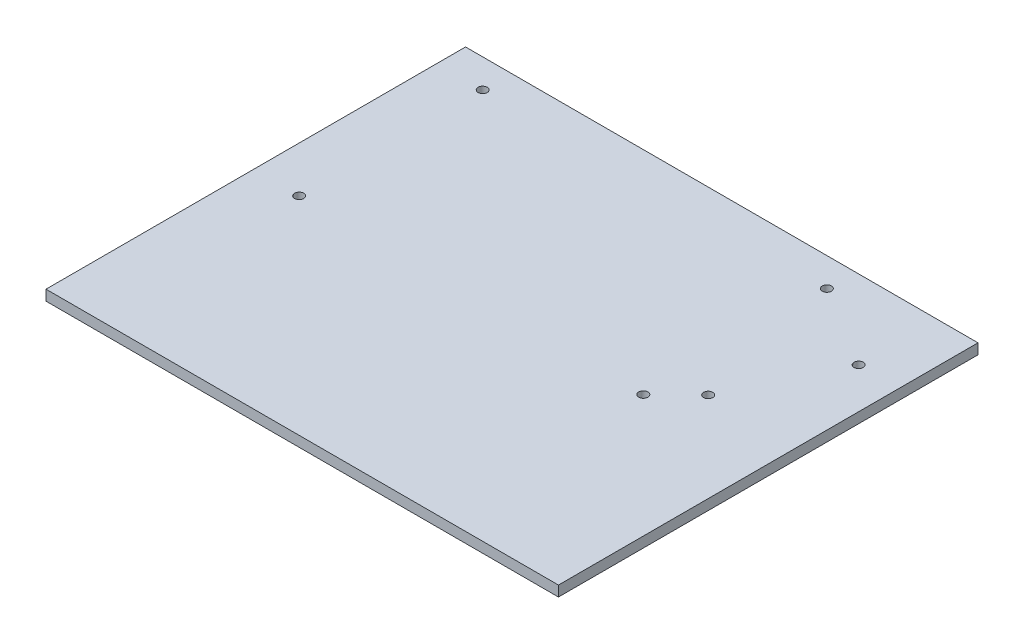
SolidWorks part; units mm, degrees
ref_plane "Front Plane" through (0, 0, 0) normal (0, 0, 1) x (1, 0, 0)
ref_plane "Top Plane" through (0, 0, 0) normal (0, 1, 0) x (1, 0, 0)
ref_plane "Right Plane" through (0, 0, 0) normal (1, 0, 0) x (0, 0, -1)
sketch "Sketch1" plane through (0, 0, 0) normal (0, 1, 0) x (1, 0, 0)
  line L1 (-62.4749, -2.9285) -> (93.8751, -2.9285)
  line L2 (-62.4749, -2.9285) -> (-62.4749, -130.9285)
  line L3 (-62.4749, -130.9285) -> (93.8751, -130.9285)
  line L4 (93.8751, -2.9285) -> (93.8751, -130.9285)
  dimension "D1" = 156.35
  dimension "D2" = 128
extrude "Boss-Extrude1" add sketch "Sketch1" along normal blind 3.175
sketch "Sketch2" plane through (0, 3.175, 0) normal (0, 1, 0) x (1, 0, 0)
  line L0 (-54.1258, -127.6508) -> (-37.2594, -127.6508)
  line L1 (-54.1258, -121.3071) -> (-54.1258, -127.6508)
  line L2 (-37.2594, -121.3071) -> (-54.1258, -121.3071)
  line L3 (-37.2594, -127.6508) -> (-37.2594, -121.3071)
  line L4 (-24.9335, -127.6508) -> (-23.2174, -127.6508)
  line L5 (-24.9335, -121.7955) -> (-24.9335, -127.6508)
  line L6 (-23.2174, -121.7955) -> (-24.9335, -121.7955)
  line L7 (-23.2174, -127.6508) -> (-23.2174, -121.7955)
  line L8 (-12.2222, -127.6508) -> (-9.9317, -127.6508)
  line L9 (-12.2222, -125.2613) -> (-12.2222, -127.6508)
  line L10 (-9.9317, -125.2613) -> (-12.2222, -125.2613)
  line L11 (-9.9317, -127.6508) -> (-9.9317, -125.2613)
  line L12 (-46.5104, -104.2192) -> (-46.5104, -107.6061)
  line L13 (-44.0104, -104.2192) -> (-46.5104, -104.2192)
  line L14 (-44.0104, -107.6061) -> (-44.0104, -104.2192)
  line L15 (-46.5104, -107.6061) -> (-44.0104, -107.6061)
  line L16 (-44.0104, -115.6057) -> (-44.0104, -111.7833)
  line L17 (-57.5314, -115.6057) -> (-44.0104, -115.6057)
  line L18 (-57.5314, -114.063) -> (-57.5314, -115.6057)
  line L19 (-46.5104, -114.063) -> (-57.5314, -114.063)
  line L20 (-46.5104, -111.7833) -> (-46.5104, -114.063)
  line L21 (-44.0104, -111.7833) -> (-46.5104, -111.7833)
  line L22 (-44.0104, -96.1003) -> (-57.5314, -96.1003)
  line L23 (-44.0104, -100.0044) -> (-44.0104, -96.1003)
  line L24 (-46.5104, -100.0044) -> (-44.0104, -100.0044)
  line L25 (-46.5104, -97.2825) -> (-46.5104, -100.0044)
  line L26 (-57.5314, -97.2825) -> (-46.5104, -97.2825)
  line L27 (-57.5314, -96.1003) -> (-57.5314, -97.2825)
  line L28 (-43.4448, -80.8491) -> (-57.3781, -80.8491)
  line L29 (-43.4448, -82.3086) -> (-43.4448, -80.8491)
  line L30 (-57.3781, -82.3086) -> (-43.4448, -82.3086)
  line L31 (-57.3781, -80.8491) -> (-57.3781, -82.3086)
  line L32 (-57.3781, -92.3628) -> (-43.4448, -92.3628)
  line L33 (-57.3781, -90.2934) -> (-57.3781, -92.3628)
  line L34 (-43.4448, -90.2934) -> (-57.3781, -90.2934)
  line L35 (-43.4448, -92.3628) -> (-43.4448, -90.2934)
  line L36 (-35.5912, -113.9129) -> (-37.0569, -113.9129)
  line L37 (-35.5912, -121.0332) -> (-35.5912, -113.9129)
  line L38 (-37.0569, -121.0332) -> (-35.5912, -121.0332)
  line L39 (-37.0569, -113.9129) -> (-37.0569, -121.0332)
  line L40 (-27.5593, -121.3071) -> (-24.7215, -121.3071)
  line L41 (-27.5593, -114.058) -> (-27.5593, -121.3071)
  line L42 (-24.7215, -114.058) -> (-27.5593, -114.058)
  line L43 (-24.7215, -121.3071) -> (-24.7215, -114.058)
  line L44 (-23.2174, -115.3264) -> (-12.1912, -115.3264)
  line L45 (-23.2174, -112.9932) -> (-23.2174, -115.3264)
  line L46 (-12.1912, -112.9932) -> (-23.2174, -112.9932)
  line L47 (-12.1912, -115.3264) -> (-12.1912, -112.9932)
  line L48 (-54.4721, -73.1649) -> (-54.4721, -74.9603)
  line L49 (62.3629, -73.1649) -> (-54.4721, -73.1649)
  line L50 (62.3629, -75.6649) -> (62.3629, -73.1649)
  line L51 (-53.9948, -75.6649) -> (62.3629, -75.6649)
  line L52 (90.4896, -128.658) -> (90.4896, -2.658)
  line L53 (88.4896, -0.658) -> (-57.5104, -0.658)
  line L54 (-59.5104, -2.658) -> (-59.5104, -128.658)
  line L55 (-57.5104, -130.658) -> (88.4896, -130.658)
  circle A0 centre (7.8765, -126.658) radius 1.6
  circle A1 centre (-56.0104, -4.158) radius 1.6
  circle A2 centre (11.845, -3.658) radius 1.6
  circle A3 centre (86.6771, -67.7415) radius 1.6
  circle A4 centre (-56.7104, -127.658) radius 1.6
  circle A5 centre (-48.5104, -11.658) radius 4
  circle A6 centre (-48.5104, -67.658) radius 4
  circle A7 centre (56.4896, -67.658) radius 4
  circle A8 centre (56.4896, -11.658) radius 4.5
  circle A9 centre (81.4896, -26.958) radius 4
  circle A10 centre (66.4896, -57.858) radius 4
  arc A11 (-54.4721, -74.9603) -> (-53.9948, -75.6649) centre (-55.5104, -76.1777) ccw
  circle A12 centre (86.9896, -4.158) radius 1.6
  circle A13 centre (87.4896, -127.658) radius 1.6
  arc A14 (90.4896, -2.658) -> (88.4896, -0.658) centre (88.4896, -2.658) ccw
  arc A15 (-57.5104, -0.658) -> (-59.5104, -2.658) centre (-57.5104, -2.658) ccw
  arc A16 (-59.5104, -128.658) -> (-57.5104, -130.658) centre (-57.5104, -128.658) ccw
  arc A17 (88.4896, -130.658) -> (90.4896, -128.658) centre (88.4896, -128.658) ccw
  circle A18 centre (56.4896, -11.658) radius 1.4
  circle A19 centre (81.4896, -26.958) radius 1.4
  circle A20 centre (66.4896, -57.858) radius 1.4
  circle A21 centre (56.4896, -67.658) radius 1.4
  circle A22 centre (-48.5104, -67.658) radius 1.4
  circle A23 centre (-48.5104, -11.658) radius 1.4
  dimension "D1" = 2.8
  dimension "D2" = 2.8
  dimension "D3" = 2.8
  dimension "D4" = 2.8
  dimension "D5" = 2.8
  dimension "D6" = 2.8
extrude "Cut-Extrude1" cut sketch "Sketch2" against normal blind 5 contours A21 | A20 | A19 | A18 | A23 | A22
